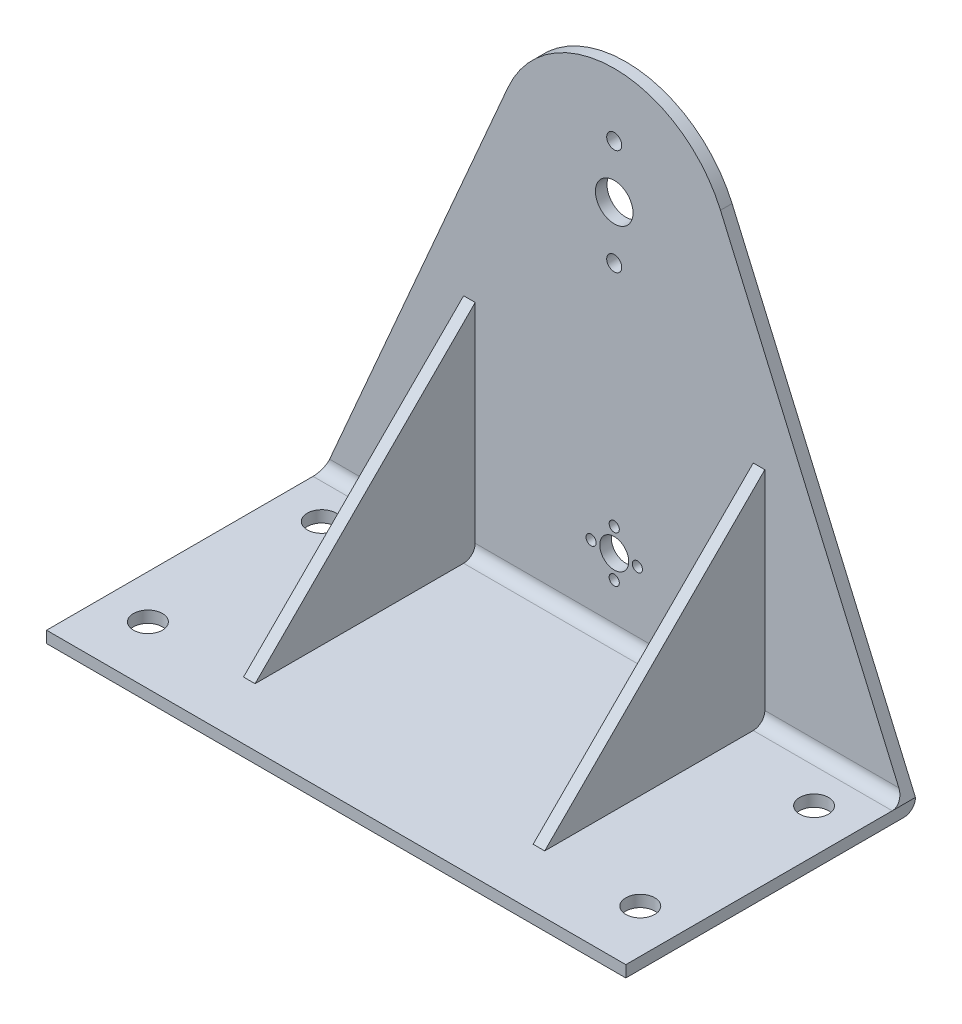
SolidWorks part; units mm, degrees
ref_plane "Front Plane" through (0, 0, 0) normal (0, 0, 1) x (1, 0, 0)
ref_plane "Top Plane" through (0, 0, 0) normal (0, 1, 0) x (1, 0, 0)
ref_plane "Right Plane" through (0, 0, 0) normal (1, 0, 0) x (0, 0, -1)
sketch "Sketch1" plane through (0, 0, 0) normal (0, 0, 1) x (1, 0, 0)
  line L0 (100, 0) -> (-100, 0)
  line L1 (0, 0) -> (0, 130) construction
  line L2 (-100, 0) -> (-36.6956, 145.9197)
  line L3 (100, 0) -> (36.6956, 145.9197)
  line L5 (100, 0) -> (-100, 0)
  line L6 (100, 0) -> (100, -4)
  line L7 (100, -4) -> (-100, -4)
  line L8 (-100, 0) -> (-100, -4)
  circle A0 centre (0, 130) radius 6.5
  circle A1 centre (0, 130) radius 40
  point P3 (0, 130)
  point P4 (0, 0)
  dimension "D2" = 13
  dimension "D4" = 80
  dimension "D1" = 200
  dimension "D3" = 130
  dimension "D5" = 4
extrude "Boss-Extrude1" add sketch "Sketch1" along normal blind 4
sketch "Sketch4" plane through (0, 0, 0) normal (0, 0, -1) x (-1, 0, 0)
  line L0 (0, 111.75) -> (0, 148.25) construction
  circle A0 centre (0, 111.75) radius 2.6
  circle A1 centre (0, 148.25) radius 2.6
  point P3 (0, 130)
  dimension "D1" = 5.2
  dimension "D2" = 36.5
extrude "Cut-Extrude1" cut sketch "Sketch4" against normal blind 10
sketch "Sketch5" plane through (0, 0, 0) normal (0, 0, -1) x (-1, 0, 0)
  line L0 (-100, 0) -> (100, 0) construction
  line L1 (-100, 0) -> (100, 0)
  line L2 (-100, -4) -> (100, -4) construction
  line L3 (-100, -4) -> (100, -4)
  line L4 (-100, 0) -> (-100, -4) construction
  line L5 (-100, 0) -> (-100, -4)
  line L6 (100, 0) -> (100, -4) construction
  line L7 (100, 0) -> (100, -4)
extrude "Boss-Extrude2" add sketch "Sketch5" against normal blind 100
fillet "Fillet1" radius 4 2 edges at (0, -4, 0) (0, 0, 4)
ref_plane "Plane1" through (-50, 0, 0) normal (-1, 0, 0) x (0, 0, 1)
ref_plane "Plane2" through (0, 0, 0) normal (-1, 0, 0) x (0, 0, 1)
sketch "Sketch8" plane through (0, 0, 0) normal (0, 1, 0) x (1, 0, 0)
  line L0 (-100, -100) -> (100, -100) construction
  line L1 (100, 0) -> (-100, 0) construction
  line L2 (100, -100) -> (100, -8) construction
  line L3 (-100, -100) -> (-100, -8) construction
  circle A0 centre (-85, -80) radius 5
  circle A1 centre (-85, -20) radius 5
  circle A2 centre (85, -80) radius 5
  circle A3 centre (85, -20) radius 5
  dimension "D1" = 20
  dimension "D2" = 20
  dimension "D3" = 20
  dimension "D4" = 20
  dimension "D5" = 15
  dimension "D6" = 15
  dimension "D7" = 15
  dimension "D8" = 15
  dimension "D9" = 10
extrude "Cut-Extrude2" cut sketch "Sketch8" against normal blind 100
sketch "Sketch9" plane through (0, 0, 4) normal (0, 0, 1) x (1, 0, 0)
  line L0 (0, 0) -> (0, 130) construction
  line L1 (100, -4) -> (-100, -4) construction
  circle A0 centre (0, 25) radius 5
  circle A1 centre (0, 33) radius 1.75
  circle A2 centre (0, 17) radius 1.75
  circle A3 centre (8, 25) radius 1.75
  circle A4 centre (-8, 25) radius 1.75
  dimension "D1" = 29
  dimension "D2" = 10
  dimension "D3" = 3.5
  dimension "D4" = 8
  dimension "D5" = 8
  dimension "D6" = 8
  dimension "D7" = 8
  dimension "D8" = 3.5
extrude "Cut-Extrude3" cut sketch "Sketch9" against normal blind 10
sketch "Sketch10" plane through (-50, 0, 0) normal (-1, 0, 0) x (0, 0, 1)
  line L0 (80, 0) -> (0, 80)
  line L1 (100, 0) -> (8, 0) construction
  line L2 (0, 0) -> (0, 145.9197) construction
  line L3 (0, 0) -> (0, 145.9197) construction
  dimension "D1" = 80
  dimension "D2" = 80
rib "Rib1" sketch "Sketch10" sketch "Sketch10" thickness 4 extrusion direction parallel to sketch draft on no parameters "D1"=4
mirror "Mirror1" about plane through (0, 0, 0) normal (1, 0, 0) of "Rib1"
